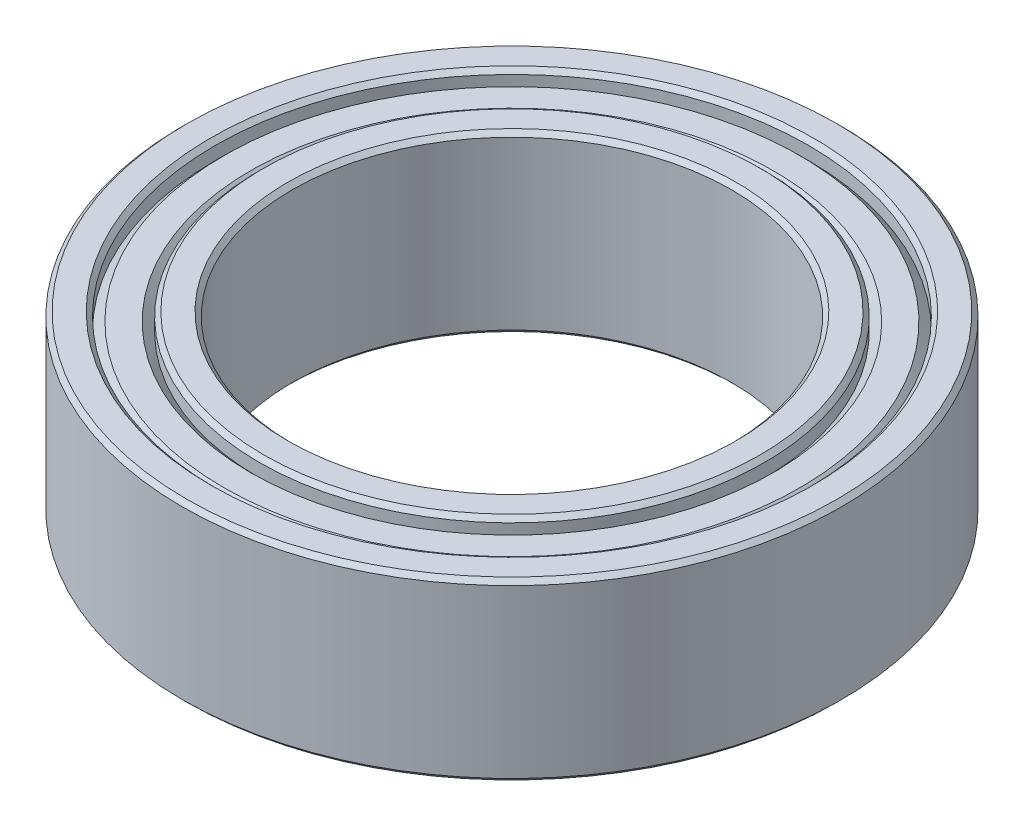
SolidWorks part; units mm, degrees
ref_plane "Front Plane" through (0, 0, 0) normal (0, 0, 1) x (1, 0, 0)
ref_plane "Top Plane" through (0, 0, 0) normal (0, 1, 0) x (1, 0, 0)
ref_plane "Right Plane" through (0, 0, 0) normal (1, 0, 0) x (0, 0, -1)
sketch "Sketch1" plane through (0, 0, 0) normal (1, 0, 0) x (0, 0, -1)
  line L1 (0, 2) -> (7.5, 2)
  line L2 (0, 2) -> (0, -2) construction
  line L3 (0, -2) -> (7.5, -2)
  line L4 (7.5, 2) -> (7.5, -2)
  line L6 (6.1, 0) -> (0, 0) construction
  line L7 (5, 2) -> (5, -2)
  dimension "D1" = 4
  dimension "D2" = 7.5
  dimension "D3" = 1.4
  dimension "D5" = 10
revolve "Revolve1" add sketch "Sketch1" angle 360 about L2
sketch "Sketch3" plane through (0, 0, 0) normal (1, 0, 0) x (0, 0, -1)
  line L0 (7.5, 2) -> (7.5, -2) construction
  line L1 (5, 2) -> (5, -2) construction
  line L2 (0, 2) -> (7.5, 2) construction
  line L3 (7.5, 2) -> (7.5, -2) construction
  line L4 (5, 2) -> (5, -2)
  line L5 (0, 2) -> (7.5, 2) construction
  line L6 (5.75, 2) -> (6.75, 2)
  line L7 (5.75, 2) -> (5.75, 1.6)
  line L8 (5.75, 1.6) -> (5.95, 1.8)
  line L9 (5.95, 1.8) -> (6.55, 1.8)
  line L10 (6.55, 1.8) -> (6.75, 1.6)
  line L11 (6.75, 1.6) -> (6.75, 2)
  line L14 (0, 2) -> (0, -2) construction
  line L17 (0, 2) -> (0, -2) construction
  line L18 (5.75, 1.6) -> (6.75, 1.6) construction
  line L19 (6.25, 1.6) -> (6.25, 2) construction
  dimension "D1" = 0.75
  dimension "D2" = 0.2
  dimension "D3" = 0.75
  dimension "D4" = 0.2
  dimension "D5" = 0.2
revolve "Cut-Revolve2" cut sketch "Sketch3" angle 360 about L17
mirror "Mirror1" about plane through (0, 0, 0) normal (0, 1, 0) of "Cut-Revolve2"
chamfer "Chamfer1" distance 0.1 angle 45 8 edges at (0, -2, 6.75) (0, 2, 6.75) (0, -2, 7.5) (0, 2, 7.5) (0, -2, 5.75) (0, 2, 5.75) (0, -2, 5) (0, 2, 5)
